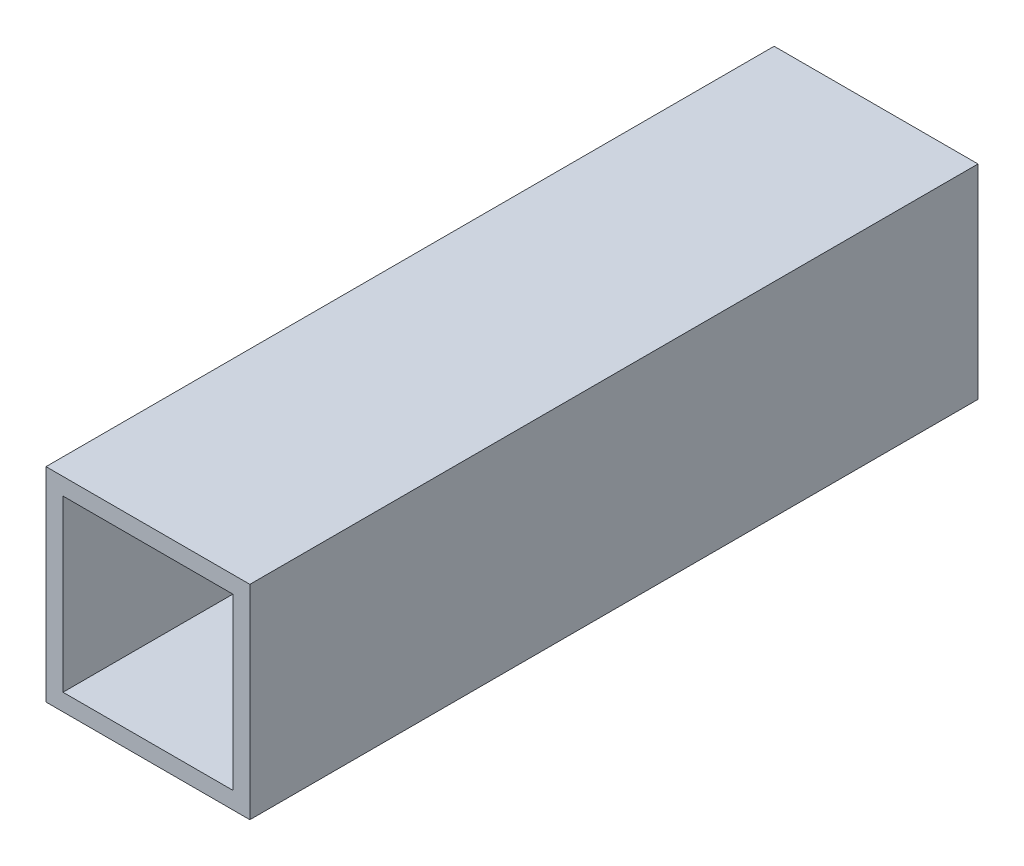
SolidWorks part; units mm, degrees
ref_plane "Ebene vorne" through (0, 0, 0) normal (0, 0, 1) x (1, 0, 0)
ref_plane "Ebene oben" through (0, 0, 0) normal (0, 1, 0) x (1, 0, 0)
ref_plane "Ebene rechts" through (0, 0, 0) normal (1, 0, 0) x (0, 0, -1)
sketch "Skizze1" plane through (0, 0, 0) normal (0, 0, 1) x (1, 0, 0)
  line L1 (6.3, -6.3) -> (-6.3, -6.3)
  line L2 (6.3, -6.3) -> (6.3, 6.3)
  line L3 (6.3, 6.3) -> (-6.3, 6.3)
  line L4 (-6.3, -6.3) -> (-6.3, 6.3)
  line L5 (6.3, -6.3) -> (-6.3, 6.3) construction
  line L6 (6.3, 6.3) -> (-6.3, -6.3) construction
  point P0 (0, 0)
  dimension "D1" = 12.6
extrude "Aufsatz-Linear austragen1" add sketch "Skizze1" along normal blind 45
sketch "Skizze2" plane through (0, 0, 45) normal (0, 0, 1) x (1, 0, 0)
  line L1 (5.25, -5.25) -> (-5.25, -5.25)
  line L2 (5.25, -5.25) -> (5.25, 5.25)
  line L3 (5.25, 5.25) -> (-5.25, 5.25)
  line L4 (-5.25, -5.25) -> (-5.25, 5.25)
  line L5 (5.25, -5.25) -> (-5.25, 5.25) construction
  line L6 (5.25, 5.25) -> (-5.25, -5.25) construction
  point P0 (0, 0)
  dimension "D1" = 10.5
extrude "Schnitt-Linear austragen1" cut sketch "Skizze2" against normal offset from surface (43.5 mm away) 1.5 up to face at (0, 0, 0)
